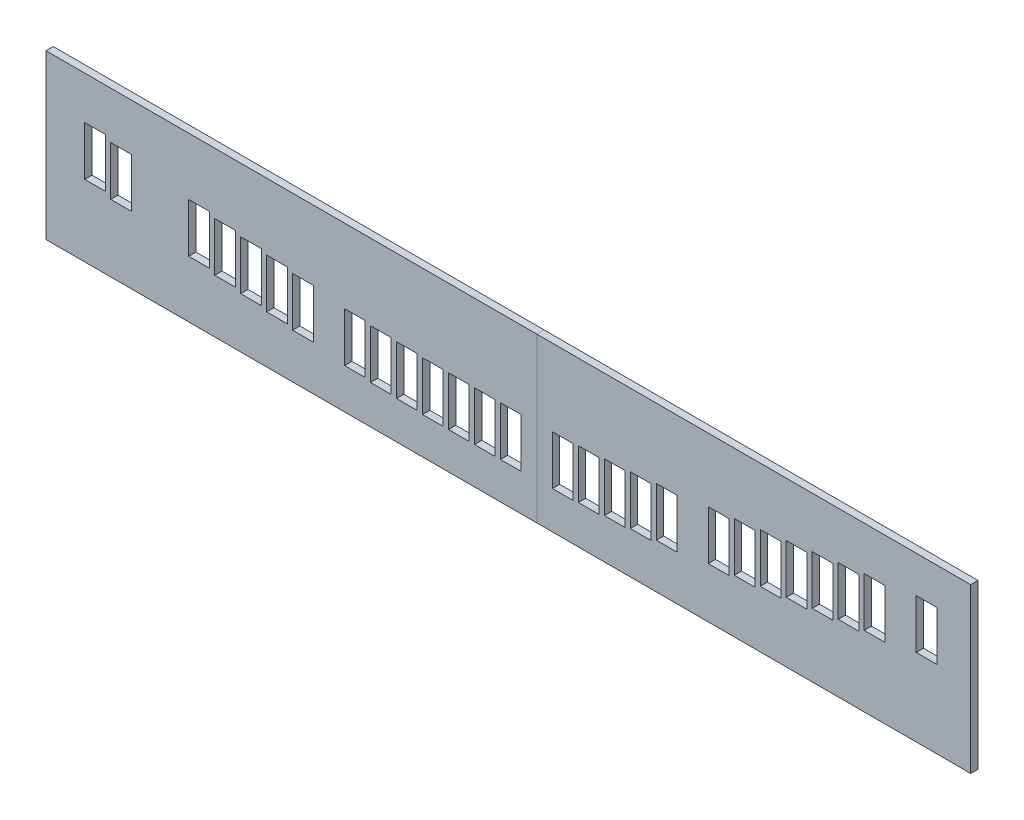
SolidWorks part; units mm, degrees
ref_plane "Front Plane" through (0, 0, 0) normal (0, 0, 1) x (1, 0, 0)
ref_plane "Top Plane" through (0, 0, 0) normal (0, 1, 0) x (1, 0, 0)
ref_plane "Right Plane" through (0, 0, 0) normal (1, 0, 0) x (0, 0, -1)
sketch "Sketch1" plane through (0, 0, 0) normal (0, 0, 1) x (1, 0, 0)
  line L0 (-0.0001, 1146.0049) -> (1685.9999, 1146.0049)
  line L1 (19.0499, 859.7049) -> (1666.8999, 859.7049)
  line L2 (-0.0001, 1146.0049) -> (-0.0001, 0)
  line L3 (19.0499, 1146.0049) -> (19.0499, 0)
  line L4 (104.9999, 1018.5049) -> (104.9999, 1092.5049)
  line L5 (104.9999, 1092.5049) -> (74.9999, 1092.5049)
  line L6 (74.9999, 1092.5049) -> (74.9999, 1018.5049)
  line L7 (74.9999, 1018.5049) -> (104.9999, 1018.5049)
  line L8 (1666.9499, 1146.0049) -> (1666.9499, 0)
  line L9 (1647.8999, 1146.0049) -> (1647.8999, 859.7049) construction
  line L10 (1685.9999, 1146.0049) -> (1685.9999, 0)
  line L11 (38.0999, 1146.0049) -> (38.0999, 859.7049) construction
  line L12 (143.9999, 992.5049) -> (173.9999, 992.5049)
  line L13 (173.9999, 992.5049) -> (173.9999, 918.5049)
  line L14 (173.9999, 918.5049) -> (143.9999, 918.5049)
  line L15 (143.9999, 918.5049) -> (143.9999, 992.5049)
  line L16 (189.9999, 992.5049) -> (219.9999, 992.5049)
  line L17 (219.9999, 992.5049) -> (219.9999, 918.5049)
  line L18 (219.9999, 918.5049) -> (189.9999, 918.5049)
  line L19 (189.9999, 918.5049) -> (189.9999, 992.5049)
  line L20 (235.9999, 992.5049) -> (265.9999, 992.5049)
  line L21 (265.9999, 992.5049) -> (265.9999, 918.5049)
  line L22 (265.9999, 918.5049) -> (235.9999, 918.5049)
  line L23 (235.9999, 918.5049) -> (235.9999, 992.5049)
  line L24 (196.9999, 1018.5049) -> (196.9999, 1092.5049)
  line L25 (196.9999, 1092.5049) -> (166.9999, 1092.5049)
  line L26 (166.9999, 1092.5049) -> (166.9999, 1018.5049)
  line L27 (166.9999, 1018.5049) -> (196.9999, 1018.5049)
  line L28 (242.9999, 1018.5049) -> (242.9999, 1092.5049)
  line L29 (242.9999, 1092.5049) -> (212.9999, 1092.5049)
  line L30 (212.9999, 1092.5049) -> (212.9999, 1018.5049)
  line L31 (212.9999, 1018.5049) -> (242.9999, 1018.5049)
  line L32 (281.9999, 992.5049) -> (311.9999, 992.5049)
  line L33 (311.9999, 992.5049) -> (311.9999, 918.5049)
  line L34 (311.9999, 918.5049) -> (281.9999, 918.5049)
  line L35 (281.9999, 918.5049) -> (281.9999, 992.5049)
  line L36 (327.9999, 992.5049) -> (357.9999, 992.5049)
  line L37 (357.9999, 992.5049) -> (357.9999, 918.5049)
  line L38 (357.9999, 918.5049) -> (327.9999, 918.5049)
  line L39 (327.9999, 918.5049) -> (327.9999, 992.5049)
  line L40 (373.9999, 992.5049) -> (403.9999, 992.5049)
  line L41 (403.9999, 992.5049) -> (403.9999, 918.5049)
  line L42 (403.9999, 918.5049) -> (373.9999, 918.5049)
  line L43 (373.9999, 918.5049) -> (373.9999, 992.5049)
  line L44 (419.9999, 992.5049) -> (449.9999, 992.5049)
  line L45 (449.9999, 992.5049) -> (449.9999, 918.5049)
  line L46 (449.9999, 918.5049) -> (419.9999, 918.5049)
  line L47 (419.9999, 918.5049) -> (419.9999, 992.5049)
  line L48 (334.9999, 1018.5049) -> (334.9999, 1092.5049)
  line L49 (334.9999, 1092.5049) -> (304.9999, 1092.5049)
  line L50 (304.9999, 1092.5049) -> (304.9999, 1018.5049)
  line L51 (304.9999, 1018.5049) -> (334.9999, 1018.5049)
  line L52 (380.9999, 1018.5049) -> (380.9999, 1092.5049)
  line L53 (380.9999, 1092.5049) -> (350.9999, 1092.5049)
  line L54 (350.9999, 1092.5049) -> (350.9999, 1018.5049)
  line L55 (350.9999, 1018.5049) -> (380.9999, 1018.5049)
  line L56 (426.9999, 1018.5049) -> (426.9999, 1092.5049)
  line L57 (426.9999, 1092.5049) -> (396.9999, 1092.5049)
  line L58 (396.9999, 1092.5049) -> (396.9999, 1018.5049)
  line L59 (396.9999, 1018.5049) -> (426.9999, 1018.5049)
  line L60 (465.9999, 992.5049) -> (495.9999, 992.5049)
  line L61 (495.9999, 992.5049) -> (495.9999, 918.5049)
  line L62 (495.9999, 918.5049) -> (465.9999, 918.5049)
  line L63 (465.9999, 918.5049) -> (465.9999, 992.5049)
  line L64 (511.9999, 992.5049) -> (541.9999, 992.5049)
  line L65 (541.9999, 992.5049) -> (541.9999, 918.5049)
  line L66 (541.9999, 918.5049) -> (511.9999, 918.5049)
  line L67 (511.9999, 918.5049) -> (511.9999, 992.5049)
  line L68 (557.9999, 992.5049) -> (587.9999, 992.5049)
  line L69 (587.9999, 992.5049) -> (587.9999, 918.5049)
  line L70 (587.9999, 918.5049) -> (557.9999, 918.5049)
  line L71 (557.9999, 918.5049) -> (557.9999, 992.5049)
  line L72 (518.9999, 1018.5049) -> (518.9999, 1092.5049)
  line L73 (518.9999, 1092.5049) -> (488.9999, 1092.5049)
  line L74 (488.9999, 1092.5049) -> (488.9999, 1018.5049)
  line L75 (488.9999, 1018.5049) -> (518.9999, 1018.5049)
  line L76 (564.9999, 1018.5049) -> (564.9999, 1092.5049)
  line L77 (564.9999, 1092.5049) -> (534.9999, 1092.5049)
  line L78 (534.9999, 1092.5049) -> (534.9999, 1018.5049)
  line L79 (534.9999, 1018.5049) -> (564.9999, 1018.5049)
  line L80 (603.9999, 992.5049) -> (633.9999, 992.5049)
  line L81 (633.9999, 992.5049) -> (633.9999, 918.5049)
  line L82 (633.9999, 918.5049) -> (603.9999, 918.5049)
  line L83 (603.9999, 918.5049) -> (603.9999, 992.5049)
  line L84 (649.9999, 992.5049) -> (679.9999, 992.5049)
  line L85 (679.9999, 992.5049) -> (679.9999, 918.5049)
  line L86 (679.9999, 918.5049) -> (649.9999, 918.5049)
  line L87 (649.9999, 918.5049) -> (649.9999, 992.5049)
  line L88 (695.9999, 992.5049) -> (725.9999, 992.5049)
  line L89 (725.9999, 992.5049) -> (725.9999, 918.5049)
  line L90 (725.9999, 918.5049) -> (695.9999, 918.5049)
  line L91 (695.9999, 918.5049) -> (695.9999, 992.5049)
  line L92 (741.9999, 992.5049) -> (771.9999, 992.5049)
  line L93 (771.9999, 992.5049) -> (771.9999, 918.5049)
  line L94 (771.9999, 918.5049) -> (741.9999, 918.5049)
  line L95 (741.9999, 918.5049) -> (741.9999, 992.5049)
  line L96 (656.9999, 1018.5049) -> (656.9999, 1092.5049)
  line L97 (656.9999, 1092.5049) -> (626.9999, 1092.5049)
  line L98 (626.9999, 1092.5049) -> (626.9999, 1018.5049)
  line L99 (626.9999, 1018.5049) -> (656.9999, 1018.5049)
  line L100 (702.9999, 1018.5049) -> (702.9999, 1092.5049)
  line L101 (702.9999, 1092.5049) -> (672.9999, 1092.5049)
  line L102 (672.9999, 1092.5049) -> (672.9999, 1018.5049)
  line L103 (672.9999, 1018.5049) -> (702.9999, 1018.5049)
  line L104 (748.9999, 1018.5049) -> (748.9999, 1092.5049)
  line L105 (748.9999, 1092.5049) -> (718.9999, 1092.5049)
  line L106 (718.9999, 1092.5049) -> (718.9999, 1018.5049)
  line L107 (718.9999, 1018.5049) -> (748.9999, 1018.5049)
  line L108 (787.9999, 992.5049) -> (817.9999, 992.5049)
  line L109 (817.9999, 992.5049) -> (817.9999, 918.5049)
  line L110 (817.9999, 918.5049) -> (787.9999, 918.5049)
  line L111 (787.9999, 918.5049) -> (787.9999, 992.5049)
  line L112 (833.9999, 992.5049) -> (863.9999, 992.5049)
  line L113 (863.9999, 992.5049) -> (863.9999, 918.5049)
  line L114 (863.9999, 918.5049) -> (833.9999, 918.5049)
  line L115 (833.9999, 918.5049) -> (833.9999, 992.5049)
  line L116 (879.9999, 992.5049) -> (909.9999, 992.5049)
  line L117 (909.9999, 992.5049) -> (909.9999, 918.5049)
  line L118 (909.9999, 918.5049) -> (879.9999, 918.5049)
  line L119 (879.9999, 918.5049) -> (879.9999, 992.5049)
  line L120 (840.9999, 1018.5049) -> (840.9999, 1092.5049)
  line L121 (840.9999, 1092.5049) -> (810.9999, 1092.5049)
  line L122 (810.9999, 1092.5049) -> (810.9999, 1018.5049)
  line L123 (810.9999, 1018.5049) -> (840.9999, 1018.5049)
  line L124 (886.9999, 1018.5049) -> (886.9999, 1092.5049)
  line L125 (886.9999, 1092.5049) -> (856.9999, 1092.5049)
  line L126 (856.9999, 1092.5049) -> (856.9999, 1018.5049)
  line L127 (856.9999, 1018.5049) -> (886.9999, 1018.5049)
  line L128 (925.9999, 992.5049) -> (955.9999, 992.5049)
  line L129 (955.9999, 992.5049) -> (955.9999, 918.5049)
  line L130 (955.9999, 918.5049) -> (925.9999, 918.5049)
  line L131 (925.9999, 918.5049) -> (925.9999, 992.5049)
  line L132 (971.9999, 992.5049) -> (1001.9999, 992.5049)
  line L133 (1001.9999, 992.5049) -> (1001.9999, 918.5049)
  line L134 (1001.9999, 918.5049) -> (971.9999, 918.5049)
  line L135 (971.9999, 918.5049) -> (971.9999, 992.5049)
  line L136 (1017.9999, 992.5049) -> (1047.9999, 992.5049)
  line L137 (1047.9999, 992.5049) -> (1047.9999, 918.5049)
  line L138 (1047.9999, 918.5049) -> (1017.9999, 918.5049)
  line L139 (1017.9999, 918.5049) -> (1017.9999, 992.5049)
  line L140 (1063.9999, 992.5049) -> (1093.9999, 992.5049)
  line L141 (1093.9999, 992.5049) -> (1093.9999, 918.5049)
  line L142 (1093.9999, 918.5049) -> (1063.9999, 918.5049)
  line L143 (1063.9999, 918.5049) -> (1063.9999, 992.5049)
  line L144 (978.9999, 1018.5049) -> (978.9999, 1092.5049)
  line L145 (978.9999, 1092.5049) -> (948.9999, 1092.5049)
  line L146 (948.9999, 1092.5049) -> (948.9999, 1018.5049)
  line L147 (948.9999, 1018.5049) -> (978.9999, 1018.5049)
  line L148 (1024.9999, 1018.5049) -> (1024.9999, 1092.5049)
  line L149 (1024.9999, 1092.5049) -> (994.9999, 1092.5049)
  line L150 (994.9999, 1092.5049) -> (994.9999, 1018.5049)
  line L151 (994.9999, 1018.5049) -> (1024.9999, 1018.5049)
  line L152 (1070.9999, 1018.5049) -> (1070.9999, 1092.5049)
  line L153 (1070.9999, 1092.5049) -> (1040.9999, 1092.5049)
  line L154 (1040.9999, 1092.5049) -> (1040.9999, 1018.5049)
  line L155 (1040.9999, 1018.5049) -> (1070.9999, 1018.5049)
  line L156 (1109.9999, 992.5049) -> (1139.9999, 992.5049)
  line L157 (1139.9999, 992.5049) -> (1139.9999, 918.5049)
  line L158 (1139.9999, 918.5049) -> (1109.9999, 918.5049)
  line L159 (1109.9999, 918.5049) -> (1109.9999, 992.5049)
  line L160 (1155.9999, 992.5049) -> (1185.9999, 992.5049)
  line L161 (1185.9999, 992.5049) -> (1185.9999, 918.5049)
  line L162 (1185.9999, 918.5049) -> (1155.9999, 918.5049)
  line L163 (1155.9999, 918.5049) -> (1155.9999, 992.5049)
  line L164 (1201.9999, 992.5049) -> (1231.9999, 992.5049)
  line L165 (1231.9999, 992.5049) -> (1231.9999, 918.5049)
  line L166 (1231.9999, 918.5049) -> (1201.9999, 918.5049)
  line L167 (1201.9999, 918.5049) -> (1201.9999, 992.5049)
  line L168 (1162.9999, 1018.5049) -> (1162.9999, 1092.5049)
  line L169 (1162.9999, 1092.5049) -> (1132.9999, 1092.5049)
  line L170 (1132.9999, 1092.5049) -> (1132.9999, 1018.5049)
  line L171 (1132.9999, 1018.5049) -> (1162.9999, 1018.5049)
  line L172 (1208.9999, 1018.5049) -> (1208.9999, 1092.5049)
  line L173 (1208.9999, 1092.5049) -> (1178.9999, 1092.5049)
  line L174 (1178.9999, 1092.5049) -> (1178.9999, 1018.5049)
  line L175 (1178.9999, 1018.5049) -> (1208.9999, 1018.5049)
  line L176 (1247.9999, 992.5049) -> (1277.9999, 992.5049)
  line L177 (1277.9999, 992.5049) -> (1277.9999, 918.5049)
  line L178 (1277.9999, 918.5049) -> (1247.9999, 918.5049)
  line L179 (1247.9999, 918.5049) -> (1247.9999, 992.5049)
  line L180 (1293.9999, 992.5049) -> (1323.9999, 992.5049)
  line L181 (1323.9999, 992.5049) -> (1323.9999, 918.5049)
  line L182 (1323.9999, 918.5049) -> (1293.9999, 918.5049)
  line L183 (1293.9999, 918.5049) -> (1293.9999, 992.5049)
  line L184 (1339.9999, 992.5049) -> (1369.9999, 992.5049)
  line L185 (1369.9999, 992.5049) -> (1369.9999, 918.5049)
  line L186 (1369.9999, 918.5049) -> (1339.9999, 918.5049)
  line L187 (1339.9999, 918.5049) -> (1339.9999, 992.5049)
  line L188 (1385.9999, 992.5049) -> (1415.9999, 992.5049)
  line L189 (1415.9999, 992.5049) -> (1415.9999, 918.5049)
  line L190 (1415.9999, 918.5049) -> (1385.9999, 918.5049)
  line L191 (1385.9999, 918.5049) -> (1385.9999, 992.5049)
  line L192 (1300.9999, 1018.5049) -> (1300.9999, 1092.5049)
  line L193 (1300.9999, 1092.5049) -> (1270.9999, 1092.5049)
  line L194 (1270.9999, 1092.5049) -> (1270.9999, 1018.5049)
  line L195 (1270.9999, 1018.5049) -> (1300.9999, 1018.5049)
  line L196 (1346.9999, 1018.5049) -> (1346.9999, 1092.5049)
  line L197 (1346.9999, 1092.5049) -> (1316.9999, 1092.5049)
  line L198 (1316.9999, 1092.5049) -> (1316.9999, 1018.5049)
  line L199 (1316.9999, 1018.5049) -> (1346.9999, 1018.5049)
  line L200 (1392.9999, 1018.5049) -> (1392.9999, 1092.5049)
  line L201 (1392.9999, 1092.5049) -> (1362.9999, 1092.5049)
  line L202 (1362.9999, 1092.5049) -> (1362.9999, 1018.5049)
  line L203 (1362.9999, 1018.5049) -> (1392.9999, 1018.5049)
  line L204 (1431.9999, 992.5049) -> (1461.9999, 992.5049)
  line L205 (1461.9999, 992.5049) -> (1461.9999, 918.5049)
  line L206 (1461.9999, 918.5049) -> (1431.9999, 918.5049)
  line L207 (1431.9999, 918.5049) -> (1431.9999, 992.5049)
  line L208 (19.1499, 330) -> (1666.9999, 330)
  line L209 (19.1499, 30) -> (1666.9999, 30)
  line L210 (38.0999, 330) -> (38.0999, 254.9027) construction
  line L211 (38.0999, 254.9027) -> (38.0999, 145.8996)
  line L212 (38.0999, 145.8996) -> (38.0999, 30) construction
  line L213 (1647.7999, 330) -> (1647.7999, 272.9027) construction
  line L214 (1647.7999, 272.9027) -> (1647.7999, 163.8996)
  line L215 (1647.7999, 163.8996) -> (1647.7999, 30) construction
  line L216 (783.9999, 97.8494) -> (783.9999, 183.5269)
  line L217 (783.9999, 183.5269) -> (819.9999, 183.5269)
  line L218 (819.9999, 183.5269) -> (819.9999, 97.8494)
  line L219 (819.9999, 97.8494) -> (783.9999, 97.8494)
  line L220 (738.7742, 97.8494) -> (738.7742, 183.5269)
  line L221 (738.7742, 183.5269) -> (774.7742, 183.5269)
  line L222 (774.7742, 183.5269) -> (774.7742, 97.8494)
  line L223 (774.7742, 97.8494) -> (738.7742, 97.8494)
  line L224 (693.5414, 97.8494) -> (693.5414, 183.5269)
  line L225 (693.5414, 183.5269) -> (729.5414, 183.5269)
  line L226 (729.5414, 183.5269) -> (729.5414, 97.8494)
  line L227 (729.5414, 97.8494) -> (693.5414, 97.8494)
  line L228 (648.31, 99.3494) -> (648.31, 185.0269)
  line L229 (648.31, 185.0269) -> (684.31, 185.0269)
  line L230 (684.31, 185.0269) -> (684.31, 99.3494)
  line L231 (684.31, 99.3494) -> (648.31, 99.3494)
  line L232 (603.0808, 100.8494) -> (603.0808, 186.5269)
  line L233 (603.0808, 186.5269) -> (639.0808, 186.5269)
  line L234 (639.0808, 186.5269) -> (639.0808, 100.8494)
  line L235 (639.0808, 100.8494) -> (603.0808, 100.8494)
  line L236 (557.849, 103.8494) -> (557.849, 189.5269)
  line L237 (557.849, 189.5269) -> (593.849, 189.5269)
  line L238 (593.849, 189.5269) -> (593.849, 103.8494)
  line L239 (593.849, 103.8494) -> (557.849, 103.8494)
  line L240 (467.3861, 111.8494) -> (467.3861, 197.5269)
  line L241 (467.3861, 197.5269) -> (503.3861, 197.5269)
  line L242 (503.3861, 197.5269) -> (503.3861, 111.8494)
  line L243 (503.3861, 111.8494) -> (467.3861, 111.8494)
  line L244 (422.1564, 116.8494) -> (422.1564, 202.5269)
  line L245 (422.1564, 202.5269) -> (458.1564, 202.5269)
  line L246 (458.1564, 202.5269) -> (458.1564, 116.8494)
  line L247 (458.1564, 116.8494) -> (422.1564, 116.8494)
  line L248 (376.927, 121.8494) -> (376.927, 207.5269)
  line L249 (376.927, 207.5269) -> (412.927, 207.5269)
  line L250 (412.927, 207.5269) -> (412.927, 121.8494)
  line L251 (412.927, 121.8494) -> (376.927, 121.8494)
  line L252 (331.6986, 126.8494) -> (331.6986, 212.5269)
  line L253 (331.6986, 212.5269) -> (367.6986, 212.5269)
  line L254 (367.6986, 212.5269) -> (367.6986, 126.8494)
  line L255 (367.6986, 126.8494) -> (331.6986, 126.8494)
  line L256 (286.4663, 132.8494) -> (286.4663, 218.5269)
  line L257 (286.4663, 218.5269) -> (322.4663, 218.5269)
  line L258 (322.4663, 218.5269) -> (322.4663, 132.8494)
  line L259 (322.4663, 132.8494) -> (286.4663, 132.8494)
  line L260 (150.7753, 150.8494) -> (150.7753, 236.5269)
  line L261 (150.7753, 236.5269) -> (186.7753, 236.5269)
  line L262 (186.7753, 236.5269) -> (186.7753, 150.8494)
  line L263 (186.7753, 150.8494) -> (150.7753, 150.8494)
  line L264 (829.2305, 97.8494) -> (829.2305, 183.5269)
  line L265 (829.2305, 183.5269) -> (865.2305, 183.5269)
  line L266 (865.2305, 183.5269) -> (865.2305, 97.8494)
  line L267 (865.2305, 97.8494) -> (829.2305, 97.8494)
  line L268 (919.6947, 99.3494) -> (919.6947, 185.0269)
  line L269 (919.6947, 185.0269) -> (955.6947, 185.0269)
  line L270 (955.6947, 185.0269) -> (955.6947, 99.3494)
  line L271 (955.6947, 99.3494) -> (919.6947, 99.3494)
  line L272 (964.9239, 100.8494) -> (964.9239, 186.5269)
  line L273 (964.9239, 186.5269) -> (1000.9239, 186.5269)
  line L274 (1000.9239, 186.5269) -> (1000.9239, 100.8494)
  line L275 (1000.9239, 100.8494) -> (964.9239, 100.8494)
  line L276 (1010.1557, 103.8494) -> (1010.1557, 189.5269)
  line L277 (1010.1557, 189.5269) -> (1046.1557, 189.5269)
  line L278 (1046.1557, 189.5269) -> (1046.1557, 103.8494)
  line L279 (1046.1557, 103.8494) -> (1010.1557, 103.8494)
  line L280 (1055.3838, 106.8494) -> (1055.3838, 192.5269)
  line L281 (1055.3838, 192.5269) -> (1091.3838, 192.5269)
  line L282 (1091.3838, 192.5269) -> (1091.3838, 106.8494)
  line L283 (1091.3838, 106.8494) -> (1055.3838, 106.8494)
  line L284 (1100.6186, 111.8494) -> (1100.6186, 197.5269)
  line L285 (1100.6186, 197.5269) -> (1136.6186, 197.5269)
  line L286 (1136.6186, 197.5269) -> (1136.6186, 111.8494)
  line L287 (1136.6186, 111.8494) -> (1100.6186, 111.8494)
  line L288 (1191.0777, 121.8494) -> (1191.0777, 207.5269)
  line L289 (1191.0777, 207.5269) -> (1227.0777, 207.5269)
  line L290 (1227.0777, 207.5269) -> (1227.0777, 121.8494)
  line L291 (1227.0777, 121.8494) -> (1191.0777, 121.8494)
  line L292 (1236.3061, 126.8494) -> (1236.3061, 212.5269)
  line L293 (1236.3061, 212.5269) -> (1272.3061, 212.5269)
  line L294 (1272.3061, 212.5269) -> (1272.3061, 126.8494)
  line L295 (1272.3061, 126.8494) -> (1236.3061, 126.8494)
  line L296 (1281.5384, 132.8494) -> (1281.5384, 218.5269)
  line L297 (1281.5384, 218.5269) -> (1317.5384, 218.5269)
  line L298 (1317.5384, 218.5269) -> (1317.5384, 132.8494)
  line L299 (1317.5384, 132.8494) -> (1281.5384, 132.8494)
  line L300 (1326.7683, 138.8494) -> (1326.7683, 224.5269)
  line L301 (1326.7683, 224.5269) -> (1362.7683, 224.5269)
  line L302 (1362.7683, 224.5269) -> (1362.7683, 138.8494)
  line L303 (1362.7683, 138.8494) -> (1326.7683, 138.8494)
  line L304 (1372.0007, 144.8494) -> (1372.0007, 230.5269)
  line L305 (1372.0007, 230.5269) -> (1408.0007, 230.5269)
  line L306 (1408.0007, 230.5269) -> (1408.0007, 144.8494)
  line L307 (1408.0007, 144.8494) -> (1372.0007, 144.8494)
  line L308 (1417.2294, 150.8494) -> (1417.2294, 236.5269)
  line L309 (1417.2294, 236.5269) -> (1453.2294, 236.5269)
  line L310 (1453.2294, 236.5269) -> (1453.2294, 150.8494)
  line L311 (1453.2294, 150.8494) -> (1417.2294, 150.8494)
  line L312 (1462.4592, 156.8494) -> (1462.4592, 242.5269)
  line L313 (1462.4592, 242.5269) -> (1498.4592, 242.5269)
  line L314 (1498.4592, 242.5269) -> (1498.4592, 156.8494)
  line L315 (1498.4592, 156.8494) -> (1462.4592, 156.8494)
  line L316 (1553.0199, 168.8494) -> (1553.0199, 254.5269)
  line L317 (1553.0199, 254.5269) -> (1589.0199, 254.5269)
  line L318 (1589.0199, 254.5269) -> (1589.0199, 168.8494)
  line L319 (1589.0199, 168.8494) -> (1553.0199, 168.8494)
sketch "Sketch2" plane through (0, 0, 0) normal (0, 0, 1) x (1, 0, 0)
  line L0 (1589.0199, 254.5269) -> (1589.0199, 168.8494) construction
  line L1 (1589.0199, 168.8494) -> (1553.0199, 168.8494) construction
  line L2 (1553.0199, 254.5269) -> (1589.0199, 254.5269) construction
  line L3 (1553.0199, 168.8494) -> (1553.0199, 254.5269) construction
  line L4 (1498.4592, 156.8494) -> (1462.4592, 156.8494) construction
  line L5 (1462.4592, 242.5269) -> (1498.4592, 242.5269) construction
  line L6 (1498.4592, 242.5269) -> (1498.4592, 156.8494) construction
  line L7 (1462.4592, 156.8494) -> (1462.4592, 242.5269) construction
  line L8 (1453.2294, 150.8494) -> (1417.2294, 150.8494) construction
  line L9 (1417.2294, 236.5269) -> (1453.2294, 236.5269) construction
  line L10 (1453.2294, 236.5269) -> (1453.2294, 150.8494) construction
  line L11 (1417.2294, 150.8494) -> (1417.2294, 236.5269) construction
  line L12 (1408.0007, 144.8494) -> (1372.0007, 144.8494) construction
  line L13 (1372.0007, 230.5269) -> (1408.0007, 230.5269) construction
  line L14 (1408.0007, 230.5269) -> (1408.0007, 144.8494) construction
  line L15 (1372.0007, 144.8494) -> (1372.0007, 230.5269) construction
  line L16 (1362.7683, 138.8494) -> (1326.7683, 138.8494) construction
  line L17 (1326.7683, 224.5269) -> (1362.7683, 224.5269) construction
  line L18 (1362.7683, 224.5269) -> (1362.7683, 138.8494) construction
  line L19 (1326.7683, 138.8494) -> (1326.7683, 224.5269) construction
  line L20 (1317.5384, 132.8494) -> (1281.5384, 132.8494) construction
  line L21 (1281.5384, 218.5269) -> (1317.5384, 218.5269) construction
  line L22 (1317.5384, 218.5269) -> (1317.5384, 132.8494) construction
  line L23 (1281.5384, 132.8494) -> (1281.5384, 218.5269) construction
  line L24 (1272.3061, 126.8494) -> (1236.3061, 126.8494) construction
  line L25 (1236.3061, 212.5269) -> (1272.3061, 212.5269) construction
  line L26 (1272.3061, 212.5269) -> (1272.3061, 126.8494) construction
  line L27 (1236.3061, 126.8494) -> (1236.3061, 212.5269) construction
  line L28 (1227.0777, 121.8494) -> (1191.0777, 121.8494) construction
  line L29 (1191.0777, 207.5269) -> (1227.0777, 207.5269) construction
  line L30 (1227.0777, 207.5269) -> (1227.0777, 121.8494) construction
  line L31 (1191.0777, 121.8494) -> (1191.0777, 207.5269) construction
  line L32 (1136.6186, 111.8494) -> (1100.6186, 111.8494) construction
  line L33 (1136.6186, 197.5269) -> (1136.6186, 111.8494) construction
  line L34 (1100.6186, 197.5269) -> (1136.6186, 197.5269) construction
  line L35 (1100.6186, 111.8494) -> (1100.6186, 197.5269) construction
  line L36 (1091.3838, 192.5269) -> (1091.3838, 106.8494) construction
  line L37 (1091.3838, 106.8494) -> (1055.3838, 106.8494) construction
  line L38 (1055.3838, 106.8494) -> (1055.3838, 192.5269) construction
  line L39 (1055.3838, 192.5269) -> (1091.3838, 192.5269) construction
  line L40 (1046.1557, 189.5269) -> (1046.1557, 103.8494) construction
  line L41 (1010.1557, 103.8494) -> (1010.1557, 189.5269) construction
  line L42 (1046.1557, 103.8494) -> (1010.1557, 103.8494) construction
  line L43 (1010.1557, 189.5269) -> (1046.1557, 189.5269) construction
  line L44 (1000.9239, 186.5269) -> (1000.9239, 100.8494) construction
  line L45 (955.6947, 185.0269) -> (955.6947, 99.3494) construction
  line L46 (964.9239, 100.8494) -> (964.9239, 186.5269) construction
  line L47 (964.9239, 186.5269) -> (1000.9239, 186.5269) construction
  line L48 (1000.9239, 100.8494) -> (964.9239, 100.8494) construction
  line L49 (955.6947, 99.3494) -> (919.6947, 99.3494) construction
  line L50 (919.6947, 185.0269) -> (955.6947, 185.0269) construction
  line L51 (919.6947, 99.3494) -> (919.6947, 185.0269) construction
  line L52 (865.2305, 97.8494) -> (829.2305, 97.8494) construction
  line L53 (829.2305, 183.5269) -> (865.2305, 183.5269) construction
  line L54 (783.9999, 183.5269) -> (819.9999, 183.5269) construction
  line L55 (819.9999, 97.8494) -> (783.9999, 97.8494) construction
  line L56 (774.7742, 97.8494) -> (738.7742, 97.8494) construction
  line L57 (738.7742, 183.5269) -> (774.7742, 183.5269) construction
  line L58 (693.5414, 183.5269) -> (729.5414, 183.5269) construction
  line L59 (729.5414, 97.8494) -> (693.5414, 97.8494) construction
  line L60 (684.31, 99.3494) -> (648.31, 99.3494) construction
  line L61 (648.31, 185.0269) -> (684.31, 185.0269) construction
  line L62 (639.0808, 100.8494) -> (603.0808, 100.8494) construction
  line L63 (593.849, 103.8494) -> (557.849, 103.8494) construction
  line L64 (603.0808, 186.5269) -> (639.0808, 186.5269) construction
  line L65 (557.849, 189.5269) -> (593.849, 189.5269) construction
  line L66 (865.2305, 183.5269) -> (865.2305, 97.8494) construction
  line L67 (829.2305, 97.8494) -> (829.2305, 183.5269) construction
  line L68 (819.9999, 183.5269) -> (819.9999, 97.8494) construction
  line L69 (783.9999, 97.8494) -> (783.9999, 183.5269) construction
  line L70 (774.7742, 183.5269) -> (774.7742, 97.8494) construction
  line L71 (738.7742, 97.8494) -> (738.7742, 183.5269) construction
  line L72 (729.5414, 183.5269) -> (729.5414, 97.8494) construction
  line L73 (693.5414, 97.8494) -> (693.5414, 183.5269) construction
  line L74 (684.31, 185.0269) -> (684.31, 99.3494) construction
  line L75 (648.31, 99.3494) -> (648.31, 185.0269) construction
  line L76 (639.0808, 186.5269) -> (639.0808, 100.8494) construction
  line L77 (603.0808, 100.8494) -> (603.0808, 186.5269) construction
  line L78 (593.849, 189.5269) -> (593.849, 103.8494) construction
  line L79 (557.849, 103.8494) -> (557.849, 189.5269) construction
  line L80 (503.3861, 197.5269) -> (503.3861, 111.8494) construction
  line L81 (322.4663, 218.5269) -> (322.4663, 132.8494) construction
  line L82 (467.3861, 111.8494) -> (467.3861, 197.5269) construction
  line L83 (467.3861, 197.5269) -> (503.3861, 197.5269) construction
  line L84 (503.3861, 111.8494) -> (467.3861, 111.8494) construction
  line L85 (458.1564, 116.8494) -> (422.1564, 116.8494) construction
  line L86 (422.1564, 202.5269) -> (458.1564, 202.5269) construction
  line L87 (458.1564, 202.5269) -> (458.1564, 116.8494) construction
  line L88 (422.1564, 116.8494) -> (422.1564, 202.5269) construction
  line L89 (412.927, 207.5269) -> (412.927, 121.8494) construction
  line L90 (376.927, 121.8494) -> (376.927, 207.5269) construction
  line L91 (412.927, 121.8494) -> (376.927, 121.8494) construction
  line L92 (376.927, 207.5269) -> (412.927, 207.5269) construction
  line L93 (367.6986, 126.8494) -> (331.6986, 126.8494) construction
  line L94 (367.6986, 212.5269) -> (367.6986, 126.8494) construction
  line L95 (331.6986, 126.8494) -> (331.6986, 212.5269) construction
  line L96 (331.6986, 212.5269) -> (367.6986, 212.5269) construction
  line L97 (322.4663, 132.8494) -> (286.4663, 132.8494) construction
  line L98 (286.4663, 218.5269) -> (322.4663, 218.5269) construction
  line L99 (286.4663, 132.8494) -> (286.4663, 218.5269) construction
  line L100 (186.7753, 150.8494) -> (150.7753, 150.8494) construction
  line L101 (150.7753, 236.5269) -> (186.7753, 236.5269) construction
  line L102 (186.7753, 236.5269) -> (186.7753, 150.8494) construction
  line L103 (150.7753, 150.8494) -> (150.7753, 236.5269) construction
  line L104 (1589.0199, 254.5269) -> (1589.0199, 168.8494)
  line L105 (1589.0199, 168.8494) -> (1553.0199, 168.8494)
  line L106 (1553.0199, 254.5269) -> (1589.0199, 254.5269)
  line L107 (1553.0199, 168.8494) -> (1553.0199, 254.5269)
  line L108 (1498.4592, 156.8494) -> (1462.4592, 156.8494)
  line L109 (1462.4592, 242.5269) -> (1498.4592, 242.5269)
  line L110 (1498.4592, 242.5269) -> (1498.4592, 156.8494)
  line L111 (1462.4592, 156.8494) -> (1462.4592, 242.5269)
  line L112 (1453.2294, 150.8494) -> (1417.2294, 150.8494)
  line L113 (1417.2294, 236.5269) -> (1453.2294, 236.5269)
  line L114 (1453.2294, 236.5269) -> (1453.2294, 150.8494)
  line L115 (1417.2294, 150.8494) -> (1417.2294, 236.5269)
  line L116 (1408.0007, 144.8494) -> (1372.0007, 144.8494)
  line L117 (1372.0007, 230.5269) -> (1408.0007, 230.5269)
  line L118 (1408.0007, 230.5269) -> (1408.0007, 144.8494)
  line L119 (1372.0007, 144.8494) -> (1372.0007, 230.5269)
  line L120 (1362.7683, 138.8494) -> (1326.7683, 138.8494)
  line L121 (1326.7683, 224.5269) -> (1362.7683, 224.5269)
  line L122 (1362.7683, 224.5269) -> (1362.7683, 138.8494)
  line L123 (1326.7683, 138.8494) -> (1326.7683, 224.5269)
  line L124 (1317.5384, 132.8494) -> (1281.5384, 132.8494)
  line L125 (1281.5384, 218.5269) -> (1317.5384, 218.5269)
  line L126 (1317.5384, 218.5269) -> (1317.5384, 132.8494)
  line L127 (1281.5384, 132.8494) -> (1281.5384, 218.5269)
  line L128 (1272.3061, 126.8494) -> (1236.3061, 126.8494)
  line L129 (1236.3061, 212.5269) -> (1272.3061, 212.5269)
  line L130 (1272.3061, 212.5269) -> (1272.3061, 126.8494)
  line L131 (1236.3061, 126.8494) -> (1236.3061, 212.5269)
  line L132 (1227.0777, 121.8494) -> (1191.0777, 121.8494)
  line L133 (1191.0777, 207.5269) -> (1227.0777, 207.5269)
  line L134 (1227.0777, 207.5269) -> (1227.0777, 121.8494)
  line L135 (1191.0777, 121.8494) -> (1191.0777, 207.5269)
  line L136 (1136.6186, 111.8494) -> (1100.6186, 111.8494)
  line L137 (1136.6186, 197.5269) -> (1136.6186, 111.8494)
  line L138 (1100.6186, 197.5269) -> (1136.6186, 197.5269)
  line L139 (1100.6186, 111.8494) -> (1100.6186, 197.5269)
  line L140 (1091.3838, 192.5269) -> (1091.3838, 106.8494)
  line L141 (1091.3838, 106.8494) -> (1055.3838, 106.8494)
  line L142 (1055.3838, 106.8494) -> (1055.3838, 192.5269)
  line L143 (1055.3838, 192.5269) -> (1091.3838, 192.5269)
  line L144 (1046.1557, 189.5269) -> (1046.1557, 103.8494)
  line L145 (1010.1557, 103.8494) -> (1010.1557, 189.5269)
  line L146 (1046.1557, 103.8494) -> (1010.1557, 103.8494)
  line L147 (1010.1557, 189.5269) -> (1046.1557, 189.5269)
  line L148 (1000.9239, 186.5269) -> (1000.9239, 100.8494)
  line L149 (955.6947, 185.0269) -> (955.6947, 99.3494)
  line L150 (964.9239, 100.8494) -> (964.9239, 186.5269)
  line L151 (964.9239, 186.5269) -> (1000.9239, 186.5269)
  line L152 (1000.9239, 100.8494) -> (964.9239, 100.8494)
  line L153 (955.6947, 99.3494) -> (919.6947, 99.3494)
  line L154 (919.6947, 185.0269) -> (955.6947, 185.0269)
  line L155 (919.6947, 99.3494) -> (919.6947, 185.0269)
  line L156 (865.2305, 97.8494) -> (829.2305, 97.8494)
  line L157 (829.2305, 183.5269) -> (865.2305, 183.5269)
  line L158 (783.9999, 183.5269) -> (819.9999, 183.5269)
  line L159 (819.9999, 97.8494) -> (783.9999, 97.8494)
  line L160 (774.7742, 97.8494) -> (738.7742, 97.8494)
  line L161 (738.7742, 183.5269) -> (774.7742, 183.5269)
  line L162 (693.5414, 183.5269) -> (729.5414, 183.5269)
  line L163 (729.5414, 97.8494) -> (693.5414, 97.8494)
  line L164 (684.31, 99.3494) -> (648.31, 99.3494)
  line L165 (648.31, 185.0269) -> (684.31, 185.0269)
  line L166 (639.0808, 100.8494) -> (603.0808, 100.8494)
  line L167 (593.849, 103.8494) -> (557.849, 103.8494)
  line L168 (603.0808, 186.5269) -> (639.0808, 186.5269)
  line L169 (557.849, 189.5269) -> (593.849, 189.5269)
  line L170 (865.2305, 183.5269) -> (865.2305, 97.8494)
  line L171 (829.2305, 97.8494) -> (829.2305, 183.5269)
  line L172 (819.9999, 183.5269) -> (819.9999, 97.8494)
  line L173 (783.9999, 97.8494) -> (783.9999, 183.5269)
  line L174 (774.7742, 183.5269) -> (774.7742, 97.8494)
  line L175 (738.7742, 97.8494) -> (738.7742, 183.5269)
  line L176 (729.5414, 183.5269) -> (729.5414, 97.8494)
  line L177 (693.5414, 97.8494) -> (693.5414, 183.5269)
  line L178 (684.31, 185.0269) -> (684.31, 99.3494)
  line L179 (648.31, 99.3494) -> (648.31, 185.0269)
  line L180 (639.0808, 186.5269) -> (639.0808, 100.8494)
  line L181 (603.0808, 100.8494) -> (603.0808, 186.5269)
  line L182 (593.849, 189.5269) -> (593.849, 103.8494)
  line L183 (557.849, 103.8494) -> (557.849, 189.5269)
  line L184 (503.3861, 197.5269) -> (503.3861, 111.8494)
  line L185 (322.4663, 218.5269) -> (322.4663, 132.8494)
  line L186 (467.3861, 111.8494) -> (467.3861, 197.5269)
  line L187 (467.3861, 197.5269) -> (503.3861, 197.5269)
  line L188 (503.3861, 111.8494) -> (467.3861, 111.8494)
  line L189 (458.1564, 116.8494) -> (422.1564, 116.8494)
  line L190 (422.1564, 202.5269) -> (458.1564, 202.5269)
  line L191 (458.1564, 202.5269) -> (458.1564, 116.8494)
  line L192 (422.1564, 116.8494) -> (422.1564, 202.5269)
  line L193 (412.927, 207.5269) -> (412.927, 121.8494)
  line L194 (376.927, 121.8494) -> (376.927, 207.5269)
  line L195 (412.927, 121.8494) -> (376.927, 121.8494)
  line L196 (376.927, 207.5269) -> (412.927, 207.5269)
  line L197 (367.6986, 126.8494) -> (331.6986, 126.8494)
  line L198 (367.6986, 212.5269) -> (367.6986, 126.8494)
  line L199 (331.6986, 126.8494) -> (331.6986, 212.5269)
  line L200 (331.6986, 212.5269) -> (367.6986, 212.5269)
  line L201 (322.4663, 132.8494) -> (286.4663, 132.8494)
  line L202 (286.4663, 218.5269) -> (322.4663, 218.5269)
  line L203 (286.4663, 132.8494) -> (286.4663, 218.5269)
  line L204 (186.7753, 150.8494) -> (150.7753, 150.8494)
  line L205 (150.7753, 236.5269) -> (186.7753, 236.5269)
  line L206 (186.7753, 236.5269) -> (186.7753, 150.8494)
  line L207 (150.7753, 150.8494) -> (150.7753, 236.5269)
  line L209 (19.0499, 1146.0049) -> (19.0499, 0) construction
  line L210 (19.0499, 318.5304) -> (1666.9499, 318.5304)
  line L211 (1666.9499, 1146.0049) -> (1666.9499, 0) construction
  line L213 (19.0499, 33.8487) -> (1666.9499, 33.8487)
  line L214 (1666.9499, 33.8487) -> (1666.9499, 318.5304)
  line L215 (19.0499, 318.5304) -> (19.0499, 33.8487)
extrude "Boss-Extrude1" add sketch "Sketch2" along normal blind 12.7
sketch "Sketch3" plane through (0, 0, 12.7) normal (0, 0, 1) x (1, 0, 0)
  line L0 (1666.9499, 318.5304) -> (19.0499, 318.5304) construction
  line L1 (1666.9499, 318.5304) -> (19.0499, 318.5304)
  line L2 (842.9999, 318.5304) -> (38.0999, 318.5304)
  line L3 (38.0999, 318.5304) -> (38.0999, 33.8487)
  line L4 (19.0499, 33.8487) -> (1666.9499, 33.8487) construction
  line L5 (38.0999, 33.8487) -> (19.0499, 33.8487)
  line L6 (19.0499, 318.5304) -> (19.0499, 33.8487) construction
  line L7 (19.0499, 33.8487) -> (19.0499, 318.5304)
  line L8 (19.0499, 318.5304) -> (38.0999, 318.5304)
  line L9 (842.9999, 318.5304) -> (1647.8999, 318.5304)
  line L10 (1647.8999, 318.5304) -> (1647.8999, 33.8487)
  line L11 (1647.8999, 33.8487) -> (1666.9499, 33.8487)
  line L12 (1666.9499, 33.8487) -> (1666.9499, 318.5304)
  line L13 (1647.8999, 318.5304) -> (1666.9499, 318.5304)
extrude "Cut-Extrude1" cut sketch "Sketch3" against normal through all contours L11 L12 L1 L10 | L7 L5 L3 L1
sketch "Sketch4" plane through (0, 0, 12.7) normal (0, 0, 1) x (1, 0, 0)
  line L0 (150.7753, 150.8494) -> (186.7753, 150.8494) construction
  line L1 (1553.0199, 168.8494) -> (1589.0199, 168.8494) construction
  line L2 (783.9999, 97.8494) -> (819.9999, 97.8494) construction
  line L3 (1647.8999, 318.5304) -> (1647.8999, 33.8487) construction
  line L4 (38.0999, 318.5304) -> (38.0999, 33.8487) construction
  line L5 (1647.8999, 318.5304) -> (1647.8999, 33.8487)
  line L6 (38.0999, 318.5304) -> (38.0999, 33.8487)
  line L7 (150.7753, 193.6881) -> (141.5453, 193.6881)
  line L8 (150.7753, 236.5269) -> (150.7753, 150.8494) construction
  line L9 (141.5453, 193.6881) -> (105.5453, 193.6881)
  line L10 (105.5453, 193.6881) -> (105.5453, 158.3386)
  line L11 (105.5453, 158.3386) -> (141.5453, 158.3386)
  line L12 (141.5453, 158.3386) -> (141.5453, 244.0186)
  line L13 (141.5453, 244.0186) -> (105.5453, 244.0186)
  line L14 (105.5453, 244.0186) -> (105.5453, 193.6881)
  arc A0 (38.0999, 170.4469) -> (1647.8999, 180.2216) centre (817.8348, 4319.7984) ccw
  point P0 (168.7753, 150.8494)
  point P1 (1571.0199, 168.8494)
  point P4 (801.9999, 97.8494)
extrude "Cut-Extrude2" cut sketch "Sketch4" against normal through all contours L13 L14 L9 L12 | L11 L12 L9 L10
sketch "Sketch5" plane through (0, 0, 12.7) normal (0, 0, 1) x (1, 0, 0)
  line L0 (865.2305, 183.5269) -> (919.6947, 185.0269)
  line L1 (892.4626, 184.2769) -> (892.4626, 33.8487)
  line L2 (38.0999, 33.8487) -> (1647.8999, 33.8487) construction
  line L3 (892.4626, 184.2769) -> (892.4626, 318.5304)
  line L4 (1647.8999, 318.5304) -> (38.0999, 318.5304) construction
ref_plane "Plane1" through (892.4626, 0, 0) normal (-1, 0, 0) x (0, 0, 1)
split "Split1" trim tools "Plane1" bodies to split 103 resulting bodies 104 105
